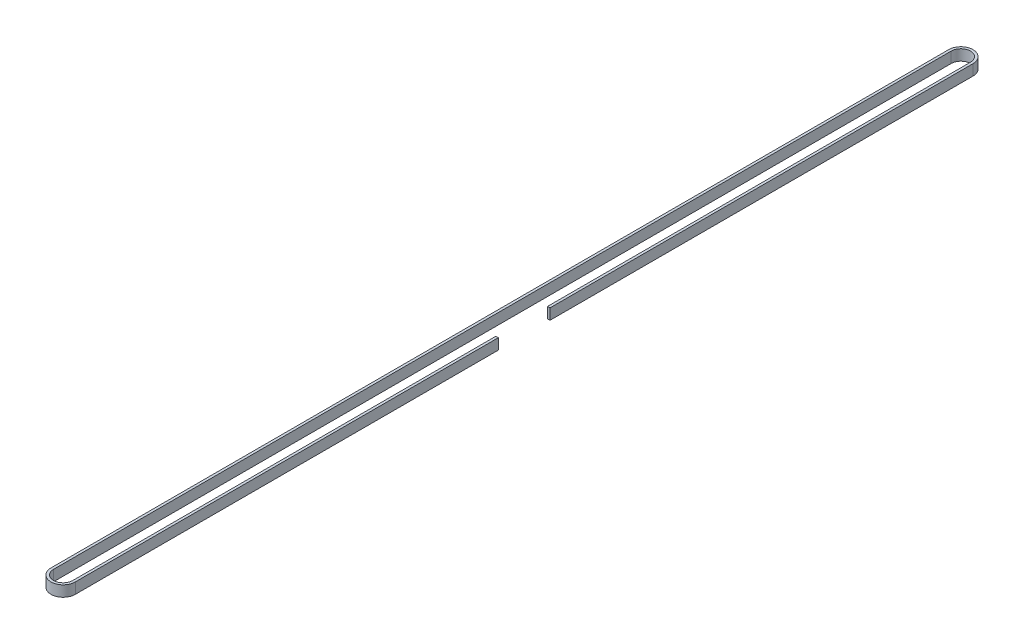
SolidWorks part; units mm, degrees
ref_plane "Front Plane" through (0, 0, 0) normal (0, 0, 1) x (1, 0, 0)
ref_plane "Top Plane" through (0, 0, 0) normal (0, 1, 0) x (1, 0, 0)
ref_plane "Right Plane" through (0, 0, 0) normal (1, 0, 0) x (0, 0, -1)
sketch "Sketch1" plane through (0, 0, 0) normal (0, 1, 0) x (1, 0, 0)
  line L0 (344.01, -294.7675) -> (344.01, 203.9825)
  line L1 (356.75, 203.9825) -> (356.75, -31.0175)
  line L2 (356.75, -294.7675) -> (356.75, -59.7675)
  arc A0 (356.75, -294.7675) -> (344.01, -294.7675) centre (350.38, -294.7675) cw
  arc A1 (356.75, 203.9825) -> (344.01, 203.9825) centre (350.38, 203.9825) ccw
  dimension "D1" = 6.37
  dimension "D2" = 498.75
  dimension "D3" = 235
extrude "Extrude-Thin1" add sketch "Sketch1" along normal blind 6 thin thin type two direction wall 0.376 second wall 1.004
